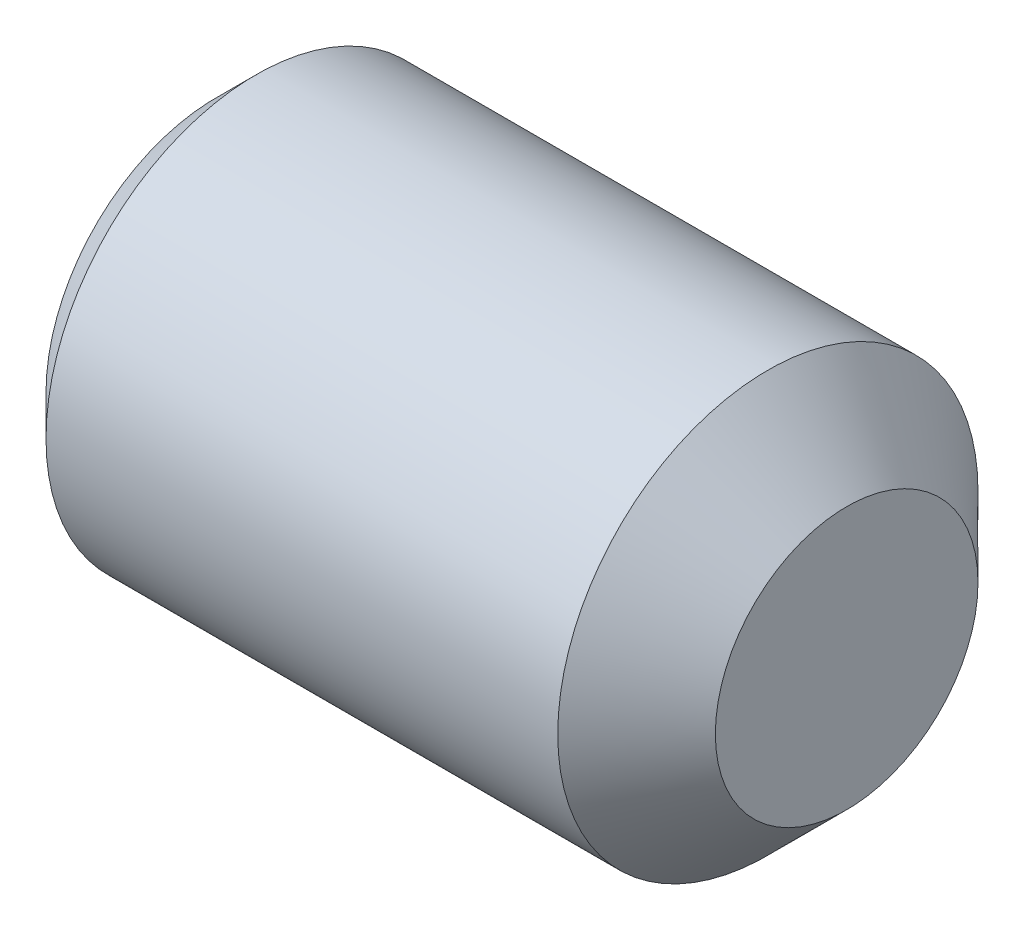
SolidWorks part; units mm, degrees
ref_plane "Front" through (0, 0, 0) normal (0, 0, 1) x (1, 0, 0)
ref_plane "Top" through (0, 0, 0) normal (0, 1, 0) x (1, 0, 0)
ref_plane "Right" through (0, 0, 0) normal (1, 0, 0) x (0, 0, -1)
sketch "Sketch1" plane through (0, 0, 0) normal (0, 0, 1) x (1, 0, 0)
  line L0 (0, 0) -> (6, 0)
  line L1 (6, 0) -> (6, 1.25)
  line L2 (6, 1.25) -> (5.25, 2)
  line L3 (5.25, 2) -> (0.379, 2)
  line L4 (0.379, 2) -> (0, 1.621)
  line L5 (0, 1.621) -> (0, 0)
  line L6 (-10.745, 0) -> (0.8952, 0) construction
  dimension "D1" = 45
  dimension "l" = 6
  dimension "D2" = 45
  dimension "dp" = 2.5
  dimension "d" = 4
  dimension "df" = 3.242
revolve "Base" add sketch "Sketch1" angle 360 about L6
cosmetic thread "ThreadCosmetic1" [suppressed] parameters "D2"=3.242
sketch "Sketch2" plane through (0, -0.0219, 0.0101) normal (-1, 0, 0) x (0, 0, 1)
  line L1 (1.1446, 0.0219) -> (0.5672, 1.0219)
  line L2 (0.5672, 1.0219) -> (-0.5875, 1.0219)
  line L3 (-0.5875, 1.0219) -> (-1.1648, 0.0219)
  line L4 (-1.1648, 0.0219) -> (-0.5875, -0.9781)
  line L5 (-0.5875, -0.9781) -> (0.5672, -0.9781)
  line L6 (0.5672, -0.9781) -> (1.1446, 0.0219)
  circle A0 centre (-0.0101, 0.0219) radius 1 construction
  dimension "s" = 2
extrude "HexagonSocket" cut sketch "Sketch2" against normal blind 1.5
sketch "Sketch3" plane through (0, 0, 0) normal (0, 0, 1) x (1, 0, 0)
  line L0 (-3.1441, 0) -> (0.1622, 0) construction
  line L2 (1.5, 1) -> (2.0774, 0)
  line L4 (1.5, 1) -> (1.5, 0)
  line L5 (1.5, 0) -> (2.0774, 0)
  dimension "D1" = 60
revolve "Cut-Revolve1" cut sketch "Sketch3" angle 360 about L0
sketch "Sketch4" plane through (0, 0, 0) normal (0, 0, 1) x (1, 0, 0)
  line L0 (0.379, 1.6718) -> (0.5685, 2)
  line L1 (0.5685, 2) -> (0.5685, 2.379)
  line L2 (0.5685, 2.379) -> (0.1895, 2.379)
  line L3 (0.1895, 2.379) -> (0.1895, 2)
  line L4 (0.1895, 2) -> (0.379, 1.6718)
  line L5 (0, 0) -> (0.9616, 0) construction
  line L6 (0.379, 2) -> (0.379, -2) construction
  dimension "D1" = 4
  dimension "D2" = 0.379
revolve "Cut-Revolve10" [suppressed] cut sketch "Sketch4" angle 360 about L5
pattern_linear "LPattern10" [suppressed] count 12 spacing 0.4548 along (1, 0, 0)
equation "\"df@Sketch1\" = \"D2@ThreadCosmetic1\""
equation "\"D1@Sketch4\" = \"d@Sketch1\""
equation "\"D2@Sketch4\" =  ( \"d@Sketch1\" - \"D2@ThreadCosmetic1\" )  / 2"
equation "\"D3@LPattern10\" = \"D2@Sketch4\" * 1.2"
equation "\"D1@LPattern10\" = (  \"l@Sketch1\" -  ( \"d@Sketch1\" - \"df@Sketch1\" )  / 2 )  / \"D3@LPattern10\""
